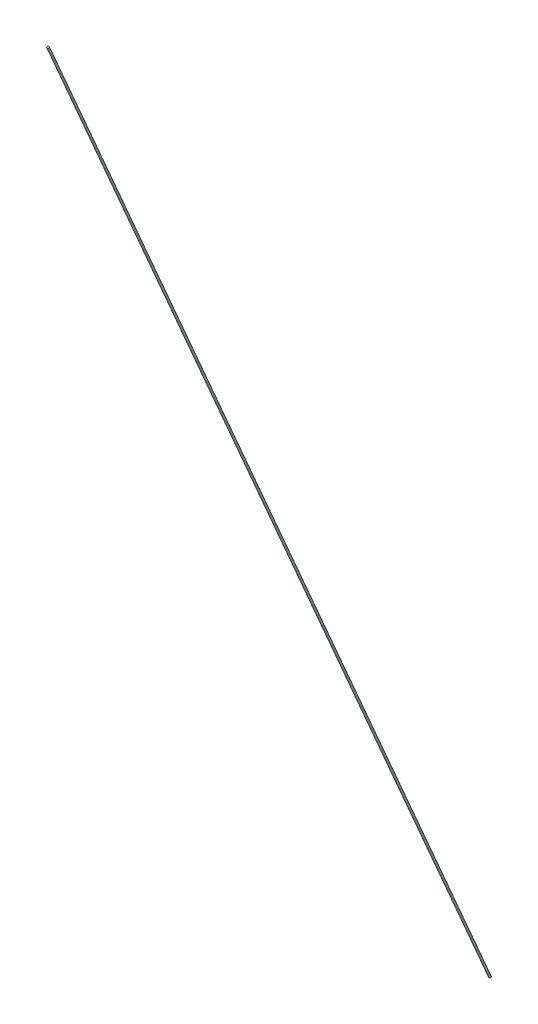
SolidWorks part; units mm, degrees
ref_plane "前视基准面" through (0, 0, 0) normal (0, 0, 1) x (1, 0, 0)
ref_plane "上视基准面" through (0, 0, 0) normal (0, 1, 0) x (1, 0, 0)
ref_plane "右视基准面" through (0, 0, 0) normal (1, 0, 0) x (0, 0, -1)
sketch "草图1" plane through (0, 0, 0) normal (0, 1, 0) x (1, 0, 0)
  line L0 (0, 0) -> (0, -217.5)
sketch "草图2" plane through (0, 0, 0) normal (0, 0, 1) x (1, 0, 0)
  line L0 (0, 0) -> (0, 500)
sketch "草图3" plane through (0, 0, 0) normal (1, 0, 0) x (0, 0, -1)
  line L9 (0, 0) -> (-217.5, 505)
sweep "扫描1" add path "草图3" circular profile diameter 1 parameters "D3"=1
